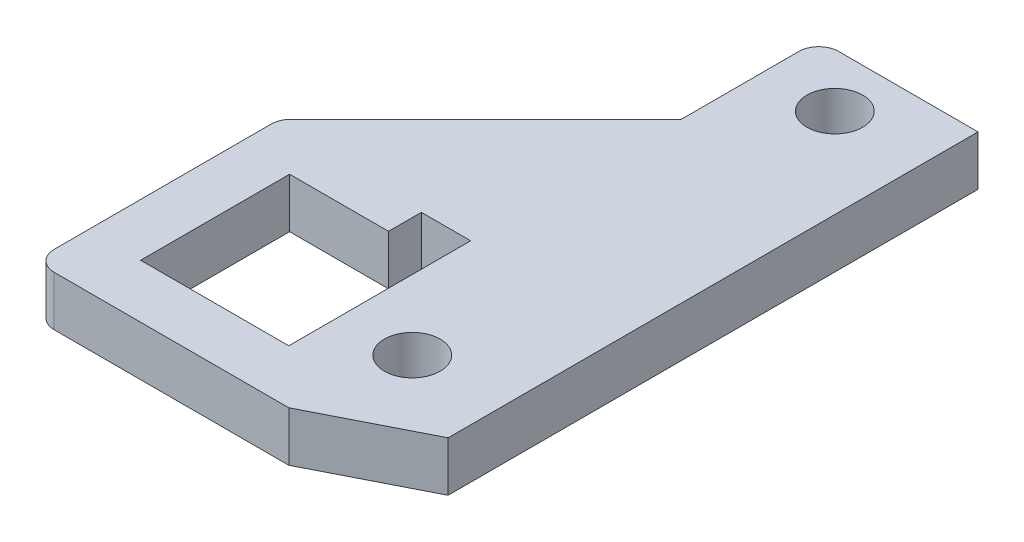
SolidWorks part; units mm, degrees
ref_plane "Front Plane" through (0, 0, 0) normal (0, 0, 1) x (1, 0, 0)
ref_plane "Top Plane" through (0, 0, 0) normal (0, 1, 0) x (1, 0, 0)
ref_plane "Right Plane" through (0, 0, 0) normal (1, 0, 0) x (0, 0, -1)
ref_plane "Plane1" through (0, 0, 0) normal (0, -1, 0) x (1, 0, 0)
sketch "Sketch1" plane through (0, 0, 0) normal (0, -1, 0) x (1, 0, 0)
  line L0 (9.6622, -12.921) -> (3.3579, -12.921)
  line L1 (3.3579, -12.921) -> (3.3579, -3.4214)
  line L2 (3.3579, -3.4214) -> (12.8041, -3.4214)
  line L3 (12.8041, -3.4214) -> (12.8041, -15.0165)
  line L4 (12.8041, -15.0165) -> (9.6622, -15.0165)
  line L5 (9.6622, -15.0165) -> (9.6622, -12.921)
  line L6 (0, -1.27) -> (0, -15.0962)
  line L7 (0.372, -15.9942) -> (12.8112, -28.4335)
  line L8 (12.8112, -28.4335) -> (12.8112, -35.9326)
  line L9 (14.0812, -37.2026) -> (22.9634, -37.2026)
  line L10 (22.9634, -37.2026) -> (22.9634, -3.4206)
  line L11 (22.9634, -3.4206) -> (16.224, 0)
  line L12 (16.224, 0) -> (1.27, 0)
  arc A0 (1.27, 0) -> (0, -1.27) centre (1.27, -1.27) ccw
  arc A1 (0, -15.0962) -> (0.372, -15.9942) centre (1.27, -15.0962) ccw
  arc A2 (12.8112, -35.9326) -> (14.0812, -37.2026) centre (14.0812, -35.9326) ccw
  circle A3 centre (17.256, -33.7812) radius 1.778
  circle A4 centre (17.256, -6.8404) radius 1.778
extrude "Boss-Extrude1" add sketch "Sketch1" against normal blind 3.175
